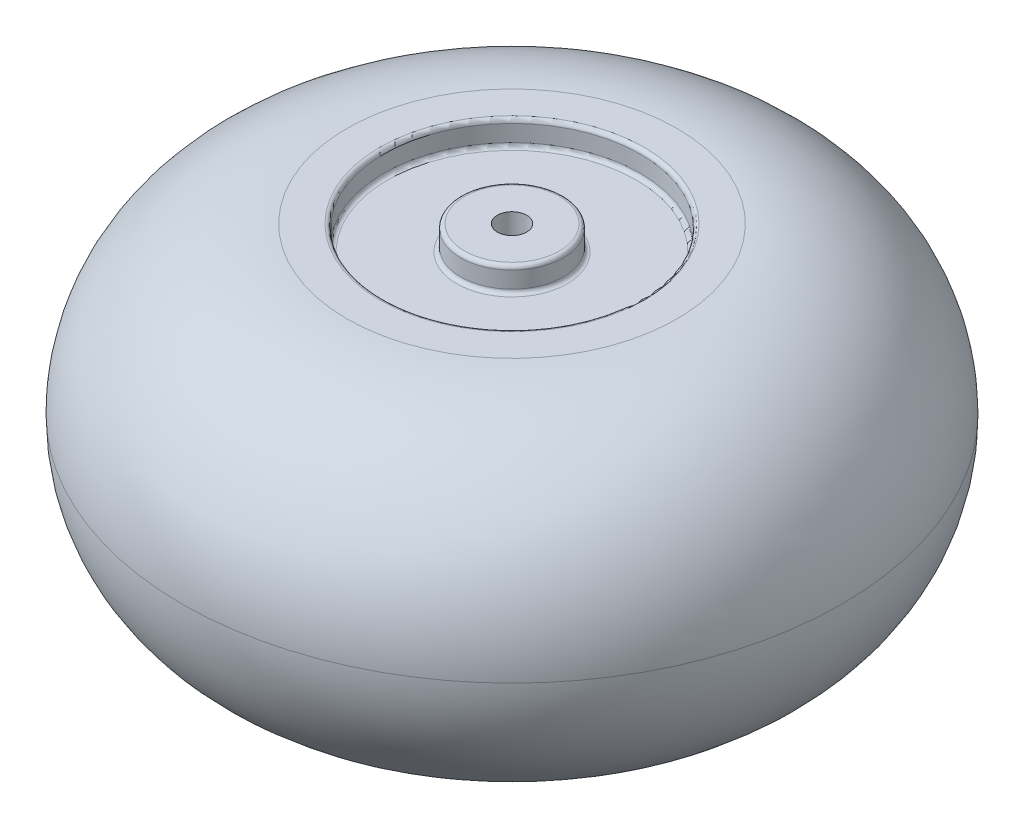
SolidWorks part; units mm, degrees
material "1060 Alloy"
ref_plane "Front Plane" through (0, 0, 0) normal (0, 0, 1) x (1, 0, 0)
ref_plane "Top Plane" through (0, 0, 0) normal (0, 1, 0) x (1, 0, 0)
ref_plane "Right Plane" through (0, 0, 0) normal (1, 0, 0) x (0, 0, -1)
sketch "Sketch3" plane through (0, 0, 0) normal (1, 0, 0) x (0, 0, -1)
  line L0 (0, 0) -> (0, 42.3409) construction
  line L1 (0, 0) -> (188.2619, 0) construction
  line L2 (6, -67.5) -> (6, 67.5)
  line L3 (6, 67.5) -> (19.3864, 67.5)
  line L4 (21, 65.8864) -> (21, 59.1136)
  line L5 (22.6136, 57.5) -> (50.9196, 57.5)
  line L6 (52.5332, 59.1136) -> (52.5332, 65.8864)
  line L7 (54.1468, 67.5) -> (67.5332, 67.5)
  line L8 (54.1468, -67.5) -> (67.5332, -67.5)
  line L9 (52.5332, -59.1136) -> (52.5332, -65.8864)
  line L10 (22.6136, -57.5) -> (50.9196, -57.5)
  line L11 (21, -65.8864) -> (21, -59.1136)
  line L12 (6, -67.5) -> (19.3864, -67.5)
  arc A0 (67.5332, 67.5) -> (134.8573, 0) centre (67.5332, 0.1756) cw
  arc A1 (67.5332, -67.5) -> (134.8573, 0) centre (67.5332, -0.1756) ccw
  arc A2 (54.1468, -67.5) -> (52.5332, -65.8864) centre (54.1468, -65.8864) cw
  arc A3 (52.5332, -59.1136) -> (50.9196, -57.5) centre (50.9196, -59.1136) ccw
  arc A4 (22.6136, -57.5) -> (21, -59.1136) centre (22.6136, -59.1136) ccw
  arc A5 (21, -65.8864) -> (19.3864, -67.5) centre (19.3864, -65.8864) cw
  arc A6 (52.5332, 65.8864) -> (54.1468, 67.5) centre (54.1468, 65.8864) cw
  arc A7 (50.9196, 57.5) -> (52.5332, 59.1136) centre (50.9196, 59.1136) ccw
  arc A8 (19.3864, 67.5) -> (21, 65.8864) centre (19.3864, 65.8864) cw
  arc A9 (21, 59.1136) -> (22.6136, 57.5) centre (22.6136, 59.1136) ccw
  point P15 (6, 0)
  point P23 (52.5332, -67.5)
  point P26 (52.5332, -57.5)
  point P29 (21, -57.5)
  point P32 (21, -67.5)
  point P35 (52.5332, 67.5)
  point P38 (52.5332, 57.5)
  point P41 (21, 67.5)
  point P44 (21, 57.5)
  dimension "D9" = 67.3244
  dimension "D1" = 6
  dimension "D2" = 15
  dimension "D3" = 67.5
  dimension "D4" = 15
  dimension "D5" = 10
  dimension "D6" = 10
  dimension "D7" = 28.306
  dimension "D8" = 1.6136
revolve "Revolve1" add sketch "Sketch3" angle 360 about L0
equation "\"wheelShaftDiameter\"= 12mm"
equation "\"D1@Sketch3\"=\"wheelShaftDiameter\"/2"
equation "\"wheelThickness\"= 135mm"
equation "\"D3@Sketch3\"=\"wheelThickness\"/2"
